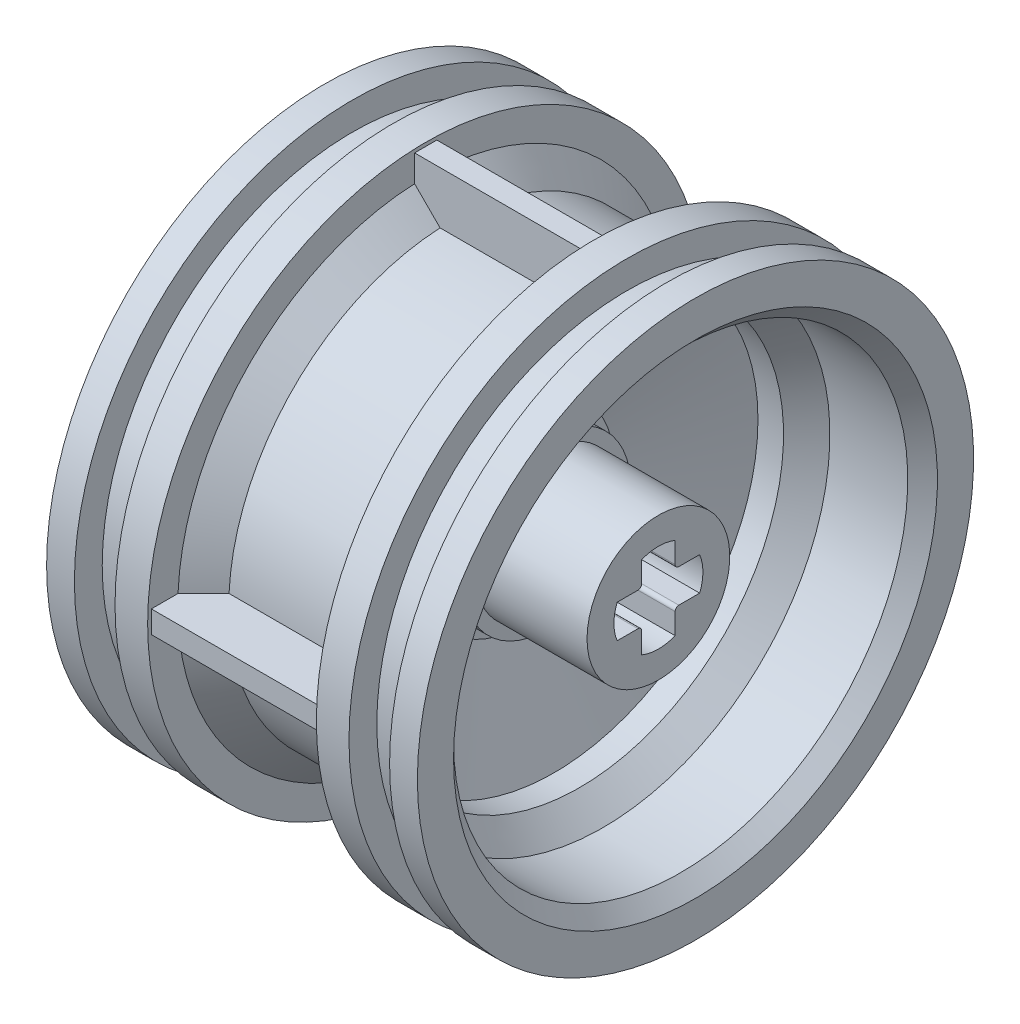
SolidWorks part; units mm, degrees
ref_plane "Front Plane" through (0, 0, 0) normal (0, 0, 1) x (1, 0, 0)
ref_plane "Top Plane" through (0, 0, 0) normal (0, 1, 0) x (1, 0, 0)
ref_plane "Right Plane" through (0, 0, 0) normal (1, 0, 0) x (0, 0, -1)
sketch "Sketch1" plane through (0, 0, 0) normal (0, 0, 1) x (1, 0, 0)
  line L0 (0, 0) -> (17.2681, 0) construction
  line L1 (0, 0) -> (0, 54.0426) construction
  line L2 (10, 12.25) -> (10, 15)
  line L3 (10, 15) -> (8.5, 15)
  line L4 (8.5, 15) -> (8.5, 13.5)
  line L5 (8.5, 13.5) -> (6.31, 13.5)
  line L6 (6.31, 13.5) -> (6.31, 15)
  line L7 (6.31, 15) -> (4.55, 15)
  line L8 (4.55, 15) -> (4.55, 13.375)
  line L9 (4.55, 13.375) -> (3.175, 12)
  line L10 (3.175, 12) -> (-3.175, 12)
  line L11 (-4.55, 13.375) -> (-3.175, 12)
  line L12 (-4.55, 15) -> (-4.55, 13.375)
  line L13 (-6.31, 15) -> (-4.55, 15)
  line L14 (-6.31, 13.5) -> (-6.31, 15)
  line L15 (-8.5, 13.5) -> (-6.31, 13.5)
  line L16 (-8.5, 15) -> (-8.5, 13.5)
  line L17 (-10, 15) -> (-8.5, 15)
  line L18 (-10, 12.25) -> (-10, 15)
  line L19 (-10, -12.25) -> (-10, -15) construction
  line L20 (-10, -15) -> (-8.5, -15) construction
  line L21 (-8.5, -15) -> (-8.5, -13.5) construction
  line L22 (-8.5, -13.5) -> (-6.31, -13.5) construction
  line L23 (-6.31, -13.5) -> (-6.31, -15) construction
  line L24 (-6.31, -15) -> (-4.55, -15) construction
  line L25 (-4.55, -15) -> (-4.55, -13.375) construction
  line L26 (-4.55, -13.375) -> (-3.175, -12) construction
  line L27 (3.175, -12) -> (-3.175, -12) construction
  line L28 (4.55, -13.375) -> (3.175, -12) construction
  line L29 (4.55, -15) -> (4.55, -13.375) construction
  line L30 (6.31, -15) -> (4.55, -15) construction
  line L31 (6.31, -13.5) -> (6.31, -15) construction
  line L32 (8.5, -13.5) -> (6.31, -13.5) construction
  line L33 (8.5, -15) -> (8.5, -13.5) construction
  line L34 (10, -15) -> (8.5, -15) construction
  line L35 (10, -12.25) -> (10, -15) construction
  line L36 (10, 12.25) -> (5, 12.25)
  line L37 (-10, 12.25) -> (-5, 12.25)
  line L38 (3.75, 11) -> (-3.75, 11)
  line L39 (3.75, -11) -> (-3.75, -11) construction
  line L40 (5, 12.25) -> (3.75, 11)
  line L41 (-5, 12.25) -> (-3.75, 11)
  point P15 (0, 12)
  dimension "D1" = 6.35
  dimension "D2" = 9.1
  dimension "D3" = 2.19
  dimension "D4" = 20
  dimension "D5" = 1.5
  dimension "D6" = 30
  dimension "D7" = 24
  dimension "D8" = 27
  dimension "D9" = 45
  dimension "D10" = 24.5
  dimension "D11" = 5
  dimension "D12" = 22
revolve "Revolve1" add sketch "Sketch1" angle 360 about L0
sketch "Sketch2" plane through (0, 0, 0) normal (0, 0, 1) x (1, 0, 0)
  line L0 (1, 11) -> (2.37, 11)
  line L1 (3.75, 11) -> (-3.75, 11) construction
  line L2 (1, 11) -> (-0.6481, 5.8)
  line L3 (-0.6481, 5.8) -> (-3.4, 5.8)
  line L4 (-3.4, 5.8) -> (-3.4, 3.805)
  line L5 (-3.4, 3.805) -> (0.6, 3.805)
  line L6 (0.6, 3.805) -> (0.6, 0)
  line L7 (0.6, 0) -> (8, 0)
  line L8 (0, 0) -> (17.2681, 0) construction
  line L9 (0, 0) -> (18.7142, 0) construction
  line L10 (8, 0) -> (8, 3.85)
  line L11 (8, 3.85) -> (2, 3.85)
  line L12 (2, 3.85) -> (2, 4.5)
  line L13 (2, 4.5) -> (0.5, 4.5)
  line L14 (0.5, 4.5) -> (0.5, 5.1)
  line L15 (0.5, 5.1) -> (2.37, 11)
  line L16 (-10, 12.25) -> (-10, 15) construction
  line L17 (10, 12.25) -> (10, 15) construction
  line L18 (8, -3.85) -> (2, -3.85) construction
  line L19 (2, -4.5) -> (0.5, -4.5) construction
  line L20 (-0.6481, -5.8) -> (-3.4, -5.8) construction
  dimension "D1" = 6.6
  dimension "D2" = 7.63
  dimension "D3" = 11
  dimension "D4" = 11.6
  dimension "D5" = 1.995
  dimension "D6" = 4
  dimension "D7" = 8
  dimension "D8" = 7.7
  dimension "D9" = 2
  dimension "D10" = 9
  dimension "D11" = 1.5
  dimension "D12" = 0.6
revolve "Revolve3" add sketch "Sketch2" angle 360 about L9
sketch "Sketch5" plane through (8, 0, 0) normal (1, 0, 0) x (0, 0, -1)
  line L0 (0, 6.2514) -> (0, 0) construction
  line L1 (0, 0) -> (7.5877, 0) construction
  line L2 (0.9, 1.1) -> (0.9, 2.2249)
  line L3 (-0.9, 1.1) -> (-0.9, 2.2249)
  line L4 (1.1, -0.9) -> (2.2249, -0.9)
  line L5 (1.1, 0.9) -> (2.2249, 0.9)
  line L6 (-0.9, -1.1) -> (-0.9, -2.2249)
  line L7 (0.9, -1.1) -> (0.9, -2.2249)
  line L8 (-1.1, 0.9) -> (-2.2249, 0.9)
  line L9 (-1.1, -0.9) -> (-2.2249, -0.9)
  arc A0 (0.9, 2.2249) -> (-0.9, 2.2249) centre (0, 0) ccw
  arc A1 (2.2249, -0.9) -> (2.2249, 0.9) centre (0, 0) ccw
  arc A2 (-0.9, -2.2249) -> (0.9, -2.2249) centre (0, 0) ccw
  arc A3 (-2.2249, 0.9) -> (-2.2249, -0.9) centre (0, 0) ccw
  arc A4 (1.1, 0.9) -> (0.9, 1.1) centre (1.1, 1.1) cw
  arc A5 (-1.1, 0.9) -> (-0.9, 1.1) centre (-1.1, 1.1) ccw
  arc A6 (-1.1, -0.9) -> (-0.9, -1.1) centre (-1.1, -1.1) cw
  arc A7 (1.1, -0.9) -> (0.9, -1.1) centre (1.1, -1.1) ccw
  circle A8 centre (0, 0) radius 3.4567 construction
  point P27 (0, 0)
  dimension "D3" = 0.2
  dimension "D2" = 2.4
  dimension "D1" = 1.8
extrude "Cut-Extrude2" cut sketch "Sketch5" against normal up to next
sketch "Sketch7" plane through (0, 0, 0) normal (0, 0, 1) x (1, 0, 0)
  line L0 (4.55, 14.8) -> (-4.55, 14.8)
  line L1 (4.55, 15) -> (4.55, -15) construction
  line L2 (-4.55, -15) -> (-4.55, 15) construction
  line L3 (0, 0) -> (15.194, 0) construction
  line L4 (4.55, -14.8) -> (-4.55, -14.8) construction
  dimension "D1" = 29.6
rib "Rib1" sketch "Sketch7" sketch "Sketch7" thickness 1.2 extrusion direction parallel to sketch draft on no parameters "D1"=1.2
pattern_circular "CirPattern1" count 4 over 360 about axis through (0, 0, 0) along (1, 0, 0) of "Rib1"
chamfer "Chamfer1" distance 0.8 angle 45 2 edges at (-10, 0, 12.25) (10, 0, 12.25)
